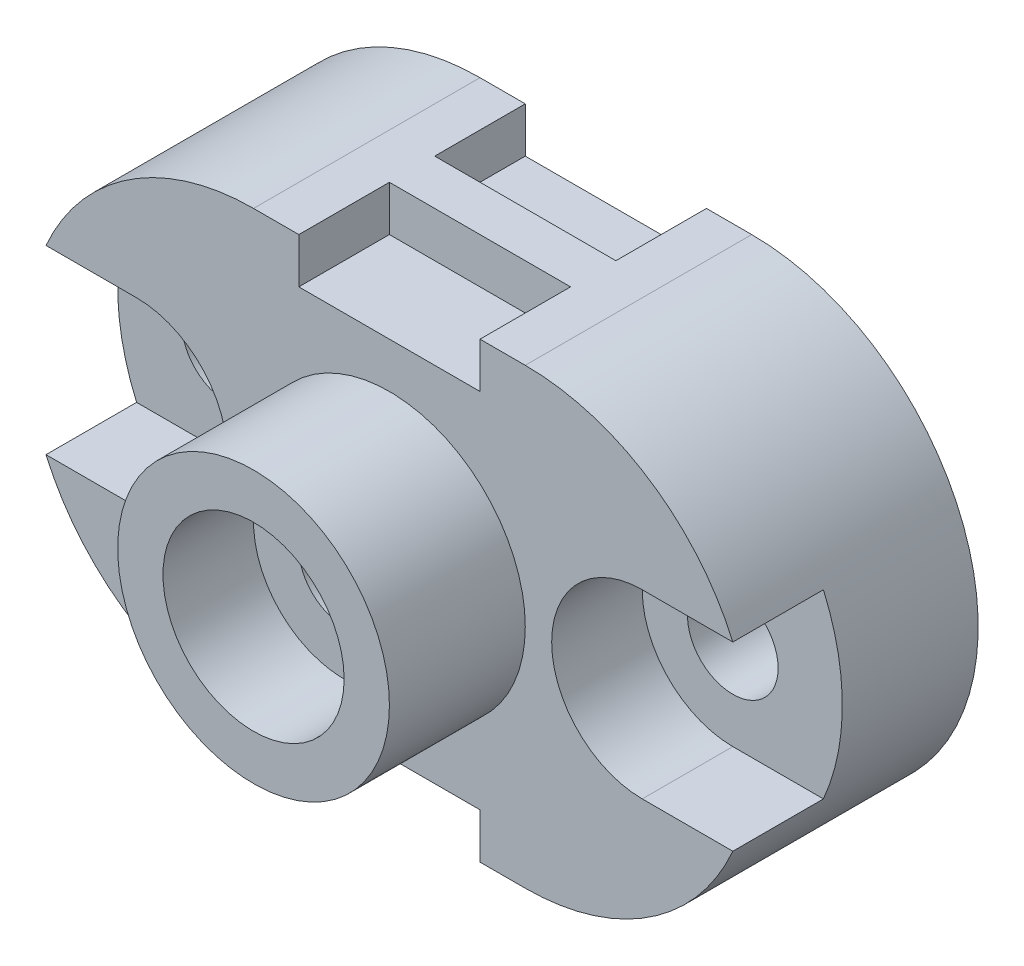
SolidWorks part; units mm, degrees
ref_plane "Front Plane" through (0, 0, 0) normal (0, 0, 1) x (1, 0, 0)
ref_plane "Top Plane" through (0, 0, 0) normal (0, 1, 0) x (1, 0, 0)
ref_plane "Right Plane" through (0, 0, 0) normal (1, 0, 0) x (0, 0, -1)
sketch "Sketch1" plane through (0, 0, 0) normal (0, 0, 1) x (1, 0, 0)
  line L0 (-30, -25) -> (0, -25) construction
  line L1 (-30, 0) -> (0, 0)
  line L2 (-30, -50) -> (0, -50)
  arc A0 (-30, 0) -> (-30, -50) centre (-30, -25) ccw
  arc A1 (0, -50) -> (0, 0) centre (0, -25) ccw
  point P2 (-15, -25)
  dimension "D2" = 25
  dimension "D1" = 30
extrude "Boss-Extrude2" add sketch "Sketch1" along normal blind 25
sketch "Sketch2" plane through (0, 0, 25) normal (0, 0, 1) x (1, 0, 0)
  line L0 (-25, 0) -> (-25, -5)
  line L1 (0, 0) -> (-30, 0) construction
  line L2 (-25, -5) -> (-5, -5)
  line L3 (-5, -5) -> (-5, 0)
  line L4 (-5, 0) -> (-25, 0)
  line L5 (-25, -50) -> (-25, -45)
  line L6 (-30, -50) -> (0, -50) construction
  line L7 (-25, -45) -> (-5, -45)
  line L8 (-5, -45) -> (-5, -50)
  line L9 (-5, -50) -> (-25, -50)
  dimension "D1" = 5
  dimension "D2" = 20
  dimension "D3" = 5
  dimension "D4" = 5
  dimension "D5" = 20
extrude "Cut-Extrude2" cut sketch "Sketch2" against normal blind 10
sketch "Sketch3" plane through (0, 0, 0) normal (0, 0, -1) x (-1, 0, 0)
  line L0 (5, 0) -> (5, -5)
  line L1 (0, 0) -> (30, 0) construction
  line L2 (5, -5) -> (25, -5)
  line L3 (25, -5) -> (25, 0)
  line L4 (25, 0) -> (5, 0)
  line L5 (5, -50) -> (5, -45)
  line L6 (30, -50) -> (0, -50) construction
  line L7 (5, -45) -> (25, -45)
  line L8 (25, -45) -> (25, -50)
  line L9 (25, -50) -> (5, -50)
  dimension "D1" = 20
  dimension "D2" = 5
  dimension "D3" = 5
  dimension "D4" = 20
  dimension "D5" = 5
extrude "Cut-Extrude3" cut sketch "Sketch3" against normal blind 10
sketch "Sketch4" plane through (0, 0, 25) normal (0, 0, 1) x (1, 0, 0)
  line L0 (-25, -5) -> (-5, -5) construction
  circle A0 centre (-15, -25) radius 15
  dimension "D1" = 30
  dimension "D2" = 20
  dimension "D3" = 10
extrude "Boss-Extrude3" add sketch "Sketch4" along normal blind 15
sketch "Sketch5" plane through (0, 0, 40) normal (0, 0, 1) x (1, 0, 0)
  circle A0 centre (-15, -25) radius 10
  dimension "D1" = 20
extrude "Cut-Extrude4" cut sketch "Sketch5" against normal blind 10
sketch "Sketch6" plane through (0, 0, 30) normal (0, 0, 1) x (1, 0, 0)
  circle A0 centre (-15, -25) radius 5
  dimension "D1" = 10
extrude "Cut-Extrude9" cut sketch "Sketch6" against normal blind 300
sketch "Sketch8" plane through (0, 0, 25) normal (0, 0, 1) x (1, 0, 0)
  line L0 (22.9129, -35) -> (12.9129, -35)
  line L1 (12.9129, -15) -> (22.9129, -15)
  line L2 (-52.9129, -15) -> (-42.9129, -15)
  line L3 (-52.9129, -35) -> (-42.9129, -35)
  arc A0 (0, -50) -> (0, 0) centre (0, -25) ccw construction
  arc A1 (12.9129, -35) -> (12.9129, -15) centre (12.9129, -25) cw
  arc A2 (22.9129, -35) -> (22.9129, -15) centre (0, -25) ccw
  arc A3 (-30, 0) -> (-30, -50) centre (-30, -25) ccw construction
  arc A4 (-42.9129, -15) -> (-42.9129, -35) centre (-42.9129, -25) cw
  arc A5 (-52.9129, -35) -> (-52.9129, -15) centre (-30, -25) cw
  point P9 (-15, -25)
  dimension "D1" = 10
  dimension "D2" = 10
  dimension "D3" = 25
  dimension "D4" = 25
  dimension "D5" = 10
  dimension "D6" = 10
extrude "Cut-Extrude10" cut sketch "Sketch8" against normal blind 10
sketch "Sketch9" plane through (0, 0, 15) normal (0, 0, 1) x (1, 0, 0)
  circle A0 centre (-42.9129, -25) radius 5
  circle A1 centre (12.9129, -25) radius 5
  point P0 (-42.9129, -25)
  point P2 (12.9129, -25)
  dimension "D1" = 10
  dimension "D2" = 10
extrude "Cut-Extrude11" cut sketch "Sketch9" against normal blind 70
